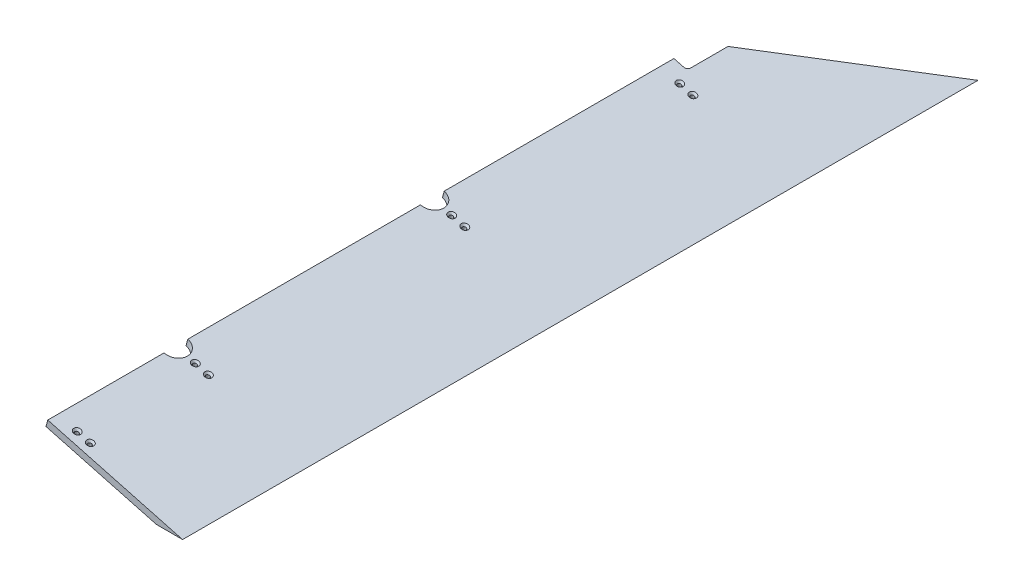
SolidWorks part; units mm, degrees
material "PE High Density"
ref_plane "Front Plane" through (0, 0, 0) normal (0, 0, 1) x (1, 0, 0)
ref_plane "Top Plane" through (0, 0, 0) normal (0, 1, 0) x (1, 0, 0)
ref_plane "Right Plane" through (0, 0, 0) normal (1, 0, 0) x (0, 0, -1)
sketch "Sketch1" plane through (0, 0, 0) normal (0, 0, 1) x (1, 0, 0)
  line L0 (0, 44.45) -> (44.45, 44.45) construction
  line L1 (0, 0) -> (44.45, 0) construction
  line L2 (0, 0) -> (0, 44.45) construction
  line L3 (0, 44.45) -> (44.45, 44.45) construction
  line L4 (44.45, 0) -> (44.45, 44.45) construction
  line L5 (45.6826, 44.2877) -> (113.7307, 26.0543) construction
  line L6 (113.7307, 26.0543) -> (114.9634, 30.6545) construction
  line L7 (114.9634, 30.6545) -> (46.9153, 48.8879) construction
  line L8 (44.45, 49.2125) -> (0, 49.2125) construction
  line L9 (0, 49.2125) -> (0, 44.45) construction
  line L10 (22.225, 55.5037) -> (229.3675, 0)
  line L11 (229.3675, 0) -> (278.4366, 0)
  line L12 (278.4366, 0) -> (25.512, 67.7709)
  line L13 (25.512, 67.7709) -> (22.225, 55.5037)
  arc A0 (45.6826, 44.2877) -> (44.45, 44.45) centre (44.45, 39.6875) ccw construction
  arc A1 (46.9153, 48.8879) -> (44.45, 49.2125) centre (44.45, 39.6875) ccw construction
  point P19 (22.225, 44.45)
  dimension "D3" = 4.7625
  dimension "D4" = 9.525
  dimension "D1" = 44.45
  dimension "D2" = 4.7625
  dimension "D5" = 44.45
  dimension "D6" = 75
  dimension "D7" = 12.7
extrude "Boss-Extrude1" add sketch "Sketch1" along normal blind 1492.25
hole_wizard "CSK for 1/4 Flat Head Socket Cap Screw1" positions "Sketch2" profile "Sketch3" countersink size "1/4" standard "ANSI Inch" end condition through all
sketch "Sketch2" plane through (18.6517, 69.6091, 0) normal (0.2588, 0.9659, 0) x (0.9659, -0.2588, 0)
  line L0 (7.1023, -1492.25) -> (7.1023, 0) construction
  line L1 (268.9491, -1492.25) -> (7.1023, -1492.25) construction
  point P0 (44.6689, -1251.7437)
  point P2 (70.0689, -1251.7437)
  point P4 (44.6689, -770.7312)
  point P6 (70.0689, -770.7312)
  point P12 (44.6689, -1473.2)
  point P14 (70.0689, -1473.2)
  point P16 (44.6689, -342.9)
  point P18 (70.0689, -342.9)
  dimension "D1" = 240.5062
  dimension "D2" = 481.0125
  dimension "D3" = 37.5666
  dimension "D4" = 25.4
  dimension "D5" = 19.05
  dimension "D6" = 1149.35
sketch "Sketch3" plane through (61.7986, 58.048, 1251.7437) normal (0, 0, 1) x (-0.9659, 0.2588, 0)
  line L0 (0, 0) -> (0, 66.3124)
  line L1 (0, 66.3124) -> (3.5712, 66.3124)
  line L2 (3.5712, 66.3124) -> (3.5712, 3.6495)
  line L3 (3.5712, 3.6495) -> (6.7437, 0)
  line L5 (6.7437, 0) -> (0, 0)
  line L6 (-3.5712, 3.6495) -> (-6.7437, 0) construction
  line L11 (0, -6.35) -> (0, 107.95) construction
  dimension "Thru Hole Dia." = 7.1425
  dimension "Thru Hole Depth" = 66.3124
  dimension "Near C'Sink Dia." = 13.4874
  dimension "Near C'Sink Angle" = 82
sketch "Sketch4" plane through (18.6517, 69.6091, 0) normal (0.2588, 0.9659, 0) x (0.9659, -0.2588, 0)
  line L0 (7.1023, -1492.25) -> (7.1023, 0) construction
  line L2 (268.9491, -1492.25) -> (7.1023, -1492.25) construction
  circle A0 centre (7.1023, -770.7312) radius 22.225
  circle A1 centre (7.1023, -1251.7437) radius 22.225
  dimension "D1" = 44.45
  dimension "D2" = 240.5062
  dimension "D3" = 481.0125
extrude "Cut-Extrude1" cut sketch "Sketch4" against normal through all
sketch "Sketch5" plane through (18.6517, 69.6091, 0) normal (0.2588, 0.9659, 0) x (0.9659, -0.2588, 0)
  line L2 (7.1023, -317.5) -> (7.1023, 0)
  line L3 (7.1023, 0) -> (268.9491, 0)
  line L5 (7.1023, -317.5) -> (32.5023, -317.5)
  line L6 (268.9491, -1492.25) -> (7.1023, -1492.25) construction
  line L7 (32.5023, -317.5) -> (32.5023, -240.61)
  line L8 (32.5023, -240.61) -> (268.9491, 0)
  line L9 (268.9491, -1492.25) -> (268.9491, 0) construction
  dimension "D1" = 44.5
  dimension "D2" = 1174.75
  dimension "D3" = 25.4
extrude "Cut-Extrude2" cut sketch "Sketch5" against normal through all
fillet "Fillet1" radius 6.35 1 edges at (48.403, 55.0633, 317.5)
